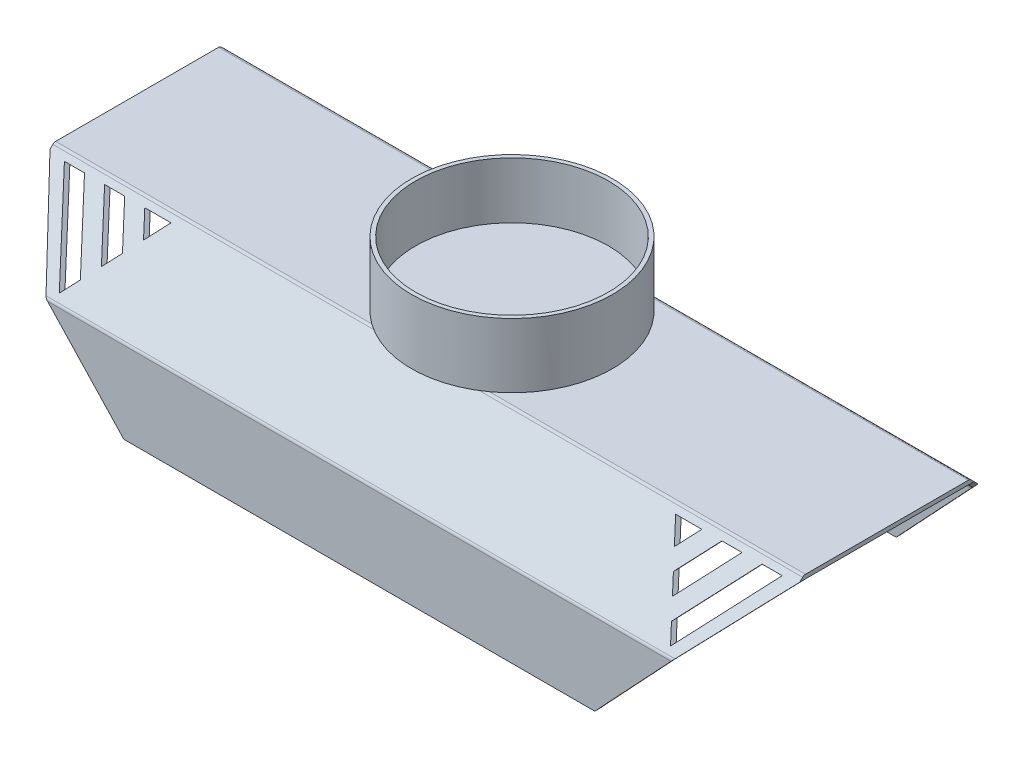
SolidWorks part; units mm, degrees
ref_plane "Front Plane" through (0, 0, 0) normal (0, 0, 1) x (1, 0, 0)
ref_plane "Top Plane" through (0, 0, 0) normal (0, 1, 0) x (1, 0, 0)
ref_plane "Right Plane" through (0, 0, 0) normal (1, 0, 0) x (0, 0, -1)
sketch "Sketch1" plane through (0, 0, 0) normal (1, 0, 0) x (0, 0, -1)
  line L0 (128.653, -19.05) -> (-128.653, -19.05)
  line L1 (126.0227, -25.4) -> (-126.0227, -25.4)
  line L2 (-241.3, -131.697) -> (-241.3, -254)
  line L3 (-133.1431, -20.9099) -> (-239.4401, -127.2069)
  line L4 (-130.5128, -27.2599) -> (-233.0901, -129.8372)
  line L5 (-234.95, -134.3273) -> (-234.95, -254)
  line L6 (-234.95, -254) -> (-241.3, -254)
  line L8 (-10.6332, -19.05) -> (-131.2832, -19.05) construction
  line L9 (-131.2832, -19.05) -> (-241.3, -129.0668) construction
  line L10 (-10.6332, -25.4) -> (-128.653, -25.4) construction
  line L11 (-128.653, -25.4) -> (-234.95, -131.697) construction
  line L12 (-241.3, -129.0668) -> (-241.3, -254) construction
  line L13 (-234.95, -131.697) -> (-234.95, -254) construction
  line L14 (0, 32.4231) -> (0, -234.95) construction
  line L15 (234.95, -254) -> (241.3, -254)
  line L16 (234.95, -134.3273) -> (234.95, -254)
  line L17 (130.5128, -27.2599) -> (233.0901, -129.8372)
  line L18 (133.1431, -20.9099) -> (239.4401, -127.2069)
  line L19 (241.3, -131.697) -> (241.3, -254)
  arc A0 (-128.653, -19.05) -> (-133.1431, -20.9099) centre (-128.653, -25.4) ccw
  arc A1 (-126.0227, -25.4) -> (-130.5128, -27.2599) centre (-126.0227, -31.75) ccw
  arc A2 (-239.4401, -127.2069) -> (-241.3, -131.697) centre (-234.95, -131.697) ccw
  arc A3 (-233.0901, -129.8372) -> (-234.95, -134.3273) centre (-228.6, -134.3273) ccw
  arc A4 (233.0901, -129.8372) -> (234.95, -134.3273) centre (228.6, -134.3273) cw
  arc A5 (239.4401, -127.2069) -> (241.3, -131.697) centre (234.95, -131.697) cw
  arc A6 (126.0227, -25.4) -> (130.5128, -27.2599) centre (126.0227, -31.75) cw
  arc A7 (128.653, -19.05) -> (133.1431, -20.9099) centre (128.653, -25.4) cw
  point P12 (-131.2832, -19.05)
  point P39 (131.2832, -19.05)
  dimension "D6" = 6.35
  dimension "D1" = 482.6
  dimension "D2" = 45
  dimension "D3" = 234.95
  dimension "D4" = 126.7931
  dimension "D5" = 6.35
extrude "Boss-Extrude1" add sketch "Sketch1" along normal mid plane 1184.91 contours A4 L16 L15 L19 A5 L18 A7 L0 A0 L3 A2 L2 L6 L5 A3 L4 A1 L1 A6 L17
sketch "Sketch2" plane through (0, 0, -241.3) normal (0, 0, -1) x (-1, 0, 0)
  line L0 (0, 91.1331) -> (0, -383.9825) construction
  line L1 (-592.455, -254) -> (-378.079, -254)
  line L2 (-592.455, -254) -> (592.455, -254) construction
  line L14 (-535.4013, -27.94) -> (-467.0802, -102.818)
  line L18 (-567.1513, -27.94) -> (-482.9552, -120.2166)
  line L19 (-482.9552, -120.2166) -> (-482.9552, 25.4643) construction
  line L20 (-398.759, -27.94) -> (-419.4552, -50.6224)
  line L21 (-398.759, -27.94) -> (-440.1513, -27.94)
  line L22 (-592.455, -19.05) -> (592.455, -19.05) construction
  line L23 (-503.6513, -27.94) -> (-451.2052, -85.4195)
  line L24 (-471.9013, -27.94) -> (-435.3302, -68.0209)
  line L25 (-440.1513, -27.94) -> (-419.4552, -50.6224)
  line L26 (-435.3302, -68.0209) -> (-451.2052, -85.4195)
  line L27 (-471.9013, -27.94) -> (-503.6513, -27.94)
  line L28 (-535.4013, -27.94) -> (-567.1513, -27.94)
  line L29 (-467.0802, -102.818) -> (-482.9552, -120.2166)
  line L30 (398.759, -27.94) -> (440.1513, -27.94)
  line L31 (440.1513, -27.94) -> (419.4552, -50.6224)
  line L32 (398.759, -27.94) -> (419.4552, -50.6224)
  line L33 (471.9013, -27.94) -> (503.6513, -27.94)
  line L34 (503.6513, -27.94) -> (451.2052, -85.4195)
  line L35 (435.3302, -68.0209) -> (451.2052, -85.4195)
  line L36 (471.9013, -27.94) -> (435.3302, -68.0209)
  line L37 (535.4013, -27.94) -> (567.1513, -27.94)
  line L38 (535.4013, -27.94) -> (467.0802, -102.818)
  line L39 (467.0802, -102.818) -> (482.9552, -120.2166)
  line L40 (567.1513, -27.94) -> (482.9552, -120.2166)
  line L41 (592.455, -25.4) -> (592.455, -254)
  line L42 (-592.455, -20.9099) -> (-592.455, -127.2069) construction
  line L43 (-592.455, -25.4) -> (-592.455, -254)
  line L44 (-592.455, -25.4) -> (-378.079, -254)
  line L45 (592.455, -254) -> (378.079, -254)
  line L46 (592.455, -25.4) -> (378.079, -254)
  dimension "D1" = 214.376
  dimension "D2" = 8.89
  dimension "D4" = 5
extrude "Cut-Extrude1" cut sketch "Sketch2" against normal up to surface (482.6 mm away) contours L43 L1 L44 | L45 L46 L41 | L18 L29 L14 L28 | L24 L26 L23 L27 | L20 L25 L21 | L37 L40 L39 L38 | L33 L34 L35 L36 | L30 L31 L32 up to face at (0, -192.8485, 241.3)
sketch "Sketch3" plane through (0, 0, -241.3) normal (0, 0, -1) x (-1, 0, 0)
  line L0 (0, 55.0601) -> (0, -340.482) construction
  line L1 (-372.1241, -260.35) -> (372.1241, -260.35)
  line L3 (-378.079, -254) -> (-372.1241, -260.35)
  line L4 (-492.772, -131.697) -> (-378.079, -254) construction
  line L5 (-378.079, -254) -> (378.079, -254) construction
  line L6 (-378.079, -254) -> (378.079, -254)
  line L7 (378.079, -254) -> (372.1241, -260.35)
  dimension "D2" = 180
extrude "Boss-Extrude2" add sketch "Sketch3" against normal up to surface (6.35 mm away) up to face at (0, -194.1636, -234.95)
sketch "Sketch4" plane through (0, 0, 241.3) normal (0, 0, 1) x (1, 0, 0)
  line L0 (-372.1241, -260.35) -> (372.1241, -260.35) construction
  line L1 (378.079, -254) -> (-378.079, -254) construction
  line L2 (-372.1241, -260.35) -> (372.1241, -260.35)
  line L3 (378.079, -254) -> (-378.079, -254)
  line L4 (-378.079, -254) -> (-372.1241, -260.35)
  line L5 (372.1241, -260.35) -> (378.079, -254)
extrude "Boss-Extrude3" add sketch "Sketch4" against normal up to surface (6.35 mm away) up to face at (0, -194.1636, 234.95)
sketch "Sketch5" plane through (0, -19.05, 0) normal (0, 1, 0) x (1, 0, 0)
  circle A0 centre (0, 0) radius 158.75
  dimension "D1" = 317.5
extrude "Boss-Extrude4" add sketch "Sketch5" along normal blind 12.7
sketch "Sketch6" plane through (0, -6.35, 0) normal (0, 1, 0) x (1, 0, 0)
  circle A0 centre (0, 0) radius 158.75
  circle A1 centre (0, 0) radius 152.4
  dimension "D1" = 304.8
  dimension "D2" = 317.5
extrude "Boss-Extrude5" add sketch "Sketch6" along normal blind 88.9
